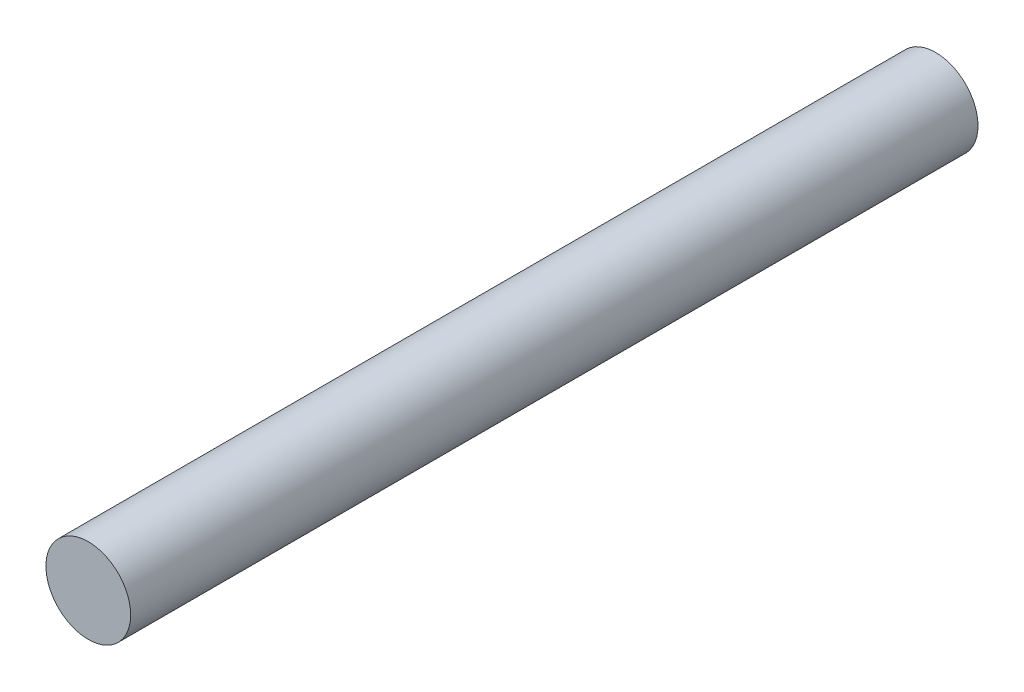
SolidWorks part; units mm, degrees
ref_plane "Front Plane" through (0, 0, 0) normal (0, 0, 1) x (1, 0, 0)
ref_plane "Top Plane" through (0, 0, 0) normal (0, 1, 0) x (1, 0, 0)
ref_plane "Right Plane" through (0, 0, 0) normal (1, 0, 0) x (0, 0, -1)
sketch "Sketch1" plane through (0, 0, 0) normal (0, 0, 1) x (1, 0, 0)
  circle A0 centre (0, 0) radius 3
  dimension "D1" = 6
extrude "Boss-Extrude1" add sketch "Sketch1" along normal blind 60
